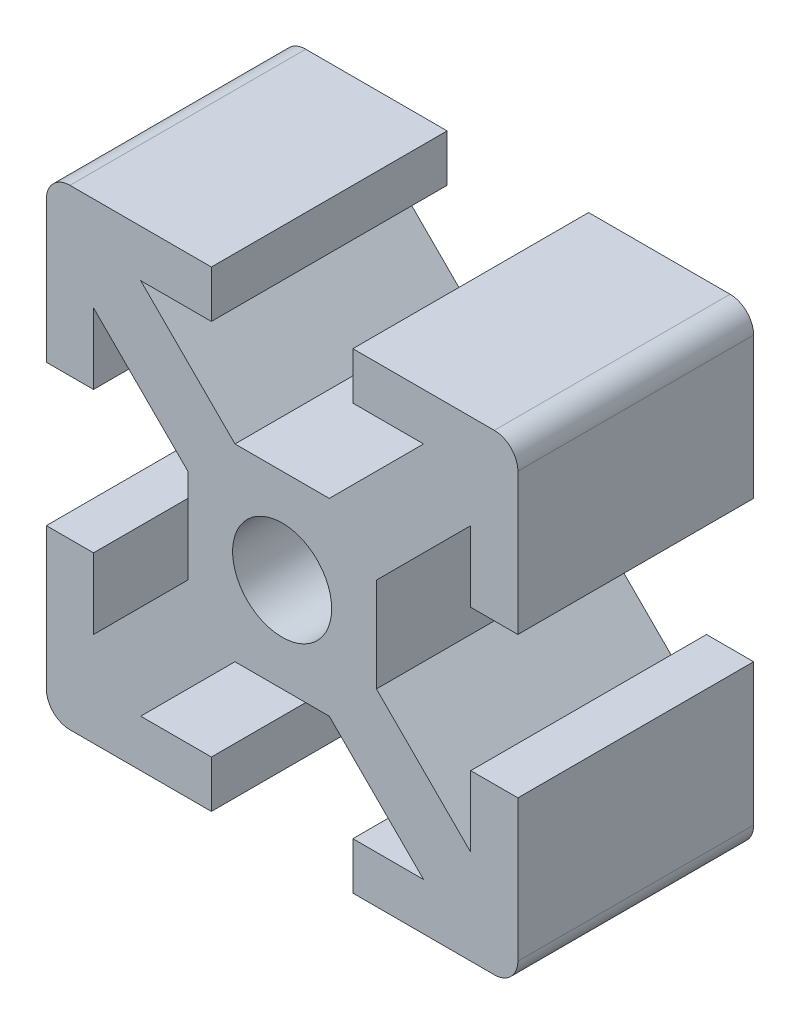
SolidWorks part; units mm, degrees
ref_plane "Front Plane" through (0, 0, 0) normal (0, 0, 1) x (1, 0, 0)
ref_plane "Top Plane" through (0, 0, 0) normal (0, 1, 0) x (1, 0, 0)
ref_plane "Right Plane" through (0, 0, 0) normal (1, 0, 0) x (0, 0, -1)
sketch "Sketch1" plane through (0, 0, 0) normal (0, 0, 1) x (1, 0, 0)
  line L0 (3, 8) -> (6, 8)
  line L1 (10, -10) -> (-10, -10)
  line L2 (10, -10) -> (10, 10)
  line L3 (10, 10) -> (-10, 10)
  line L4 (-10, -10) -> (-10, 10)
  line L5 (10, -10) -> (-10, 10) construction
  line L6 (10, 10) -> (-10, -10) construction
  line L7 (3, 10) -> (-3, 10)
  line L8 (3, 10) -> (3, 8)
  line L9 (3, 8) -> (-3, 8)
  line L10 (-3, 10) -> (-3, 8)
  line L11 (6, 8) -> (2, 4)
  line L12 (2, 4) -> (-2, 4)
  line L13 (-2, 4) -> (-6, 8)
  line L14 (-6, 8) -> (-3, 8)
  line L15 (0, 4) -> (0, 8) construction
  line L16 (10, -3) -> (8, -3)
  line L17 (10, -3) -> (10, 3)
  line L18 (10, 3) -> (8, 3)
  line L19 (8, -3) -> (8, 3)
  line L20 (4, 2) -> (8, 6)
  line L21 (8, 6) -> (8, 3)
  line L22 (4, -2) -> (4, 2)
  line L23 (8, -6) -> (4, -2)
  line L24 (8, -3) -> (8, -6)
  line L25 (-3, -10) -> (-3, -8)
  line L26 (-3, -10) -> (3, -10)
  line L27 (3, -10) -> (3, -8)
  line L28 (-3, -8) -> (3, -8)
  line L29 (2, -4) -> (6, -8)
  line L30 (6, -8) -> (3, -8)
  line L31 (-2, -4) -> (2, -4)
  line L32 (-6, -8) -> (-2, -4)
  line L33 (-3, -8) -> (-6, -8)
  line L34 (-10, 3) -> (-8, 3)
  line L35 (-10, 3) -> (-10, -3)
  line L36 (-10, -3) -> (-8, -3)
  line L37 (-8, 3) -> (-8, -3)
  line L38 (-4, -2) -> (-8, -6)
  line L39 (-8, -6) -> (-8, -3)
  line L40 (-4, 2) -> (-4, -2)
  line L41 (-8, 6) -> (-4, 2)
  line L42 (-8, 3) -> (-8, 6)
  circle A0 centre (0, 0) radius 2.1
  point P0 (0, 0)
  point P19 (-14.0153, -8.0153)
  point P20 (0, 0)
  point P44 (0, 0)
  dimension "D1" = 4.2
  dimension "D2" = 20
  dimension "D3" = 7
  dimension "D4" = 7
  dimension "D5" = 2
  dimension "D6" = 4
  dimension "D7" = 12
  dimension "D8" = 4
extrude "Boss-Extrude1" add sketch "Sketch1" along normal blind 10 contours L34 L42 L41 L40 L38 L39 L36 L4 L1 L25 L33 L32 L31 L29 L30 L27 L2 L16 L24 L23 L22 L20 L21 L18 L3 L8 L0 L11 L12 L13 L14 L10 A0
fillet "Fillet1" radius 1 4 edges at (-10, 10, 5) (-10, -10, 5) (10, 10, 5) (10, -10, 5)
